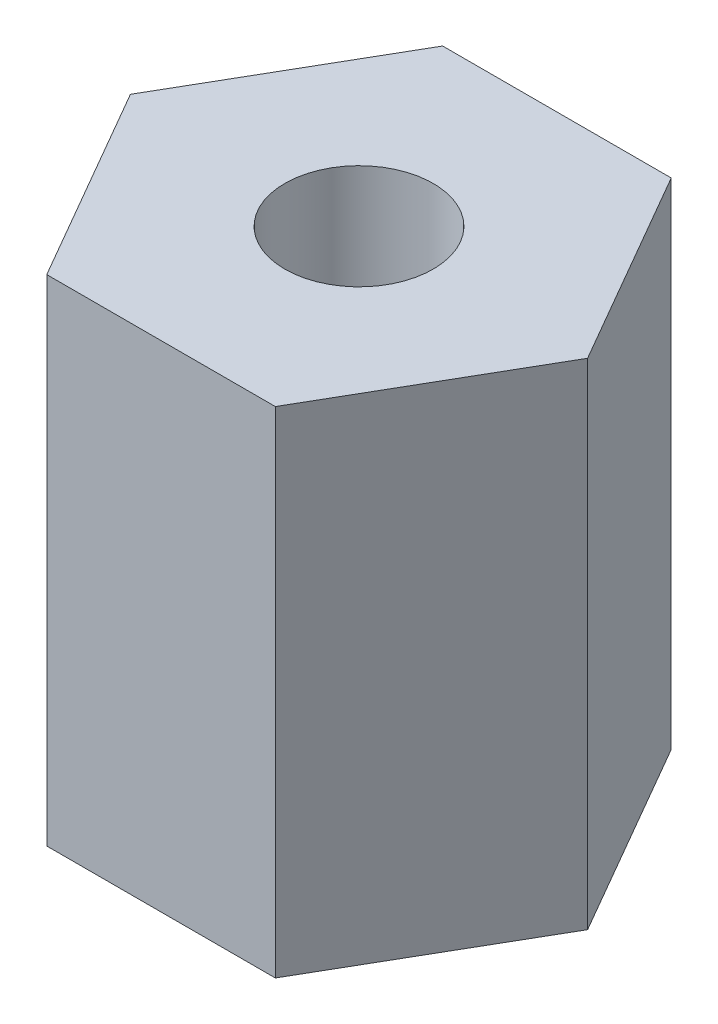
SolidWorks part; units mm, degrees
ref_plane "Front Plane" through (0, 0, 0) normal (0, 0, 1) x (1, 0, 0)
ref_plane "Top Plane" through (0, 0, 0) normal (0, 1, 0) x (1, 0, 0)
ref_plane "Right Plane" through (0, 0, 0) normal (1, 0, 0) x (0, 0, -1)
sketch "Sketch1" plane through (0, 0, 0) normal (0, 1, 0) x (1, 0, 0)
  line L1 (4.6188, 0) -> (2.3094, 4)
  line L2 (2.3094, 4) -> (-2.3094, 4)
  line L3 (-2.3094, 4) -> (-4.6188, 0)
  line L4 (-4.6188, 0) -> (-2.3094, -4)
  line L5 (-2.3094, -4) -> (2.3094, -4)
  line L6 (2.3094, -4) -> (4.6188, 0)
  circle A0 centre (0, 0) radius 4 construction
  circle A1 centre (0, 0) radius 1.5
  dimension "D2" = 3
  dimension "D1" = 8
extrude "Boss-Extrude1" add sketch "Sketch1" along normal blind 10
